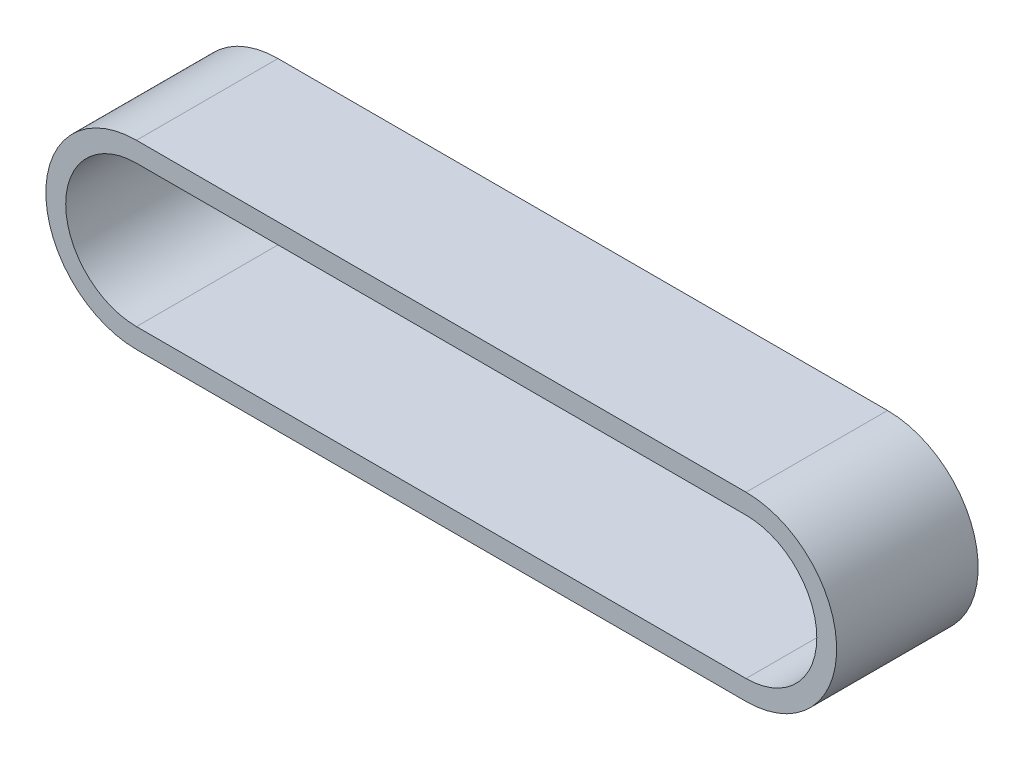
SolidWorks part; units mm, degrees
ref_plane "Plano frontal" through (0, 0, 0) normal (0, 0, 1) x (1, 0, 0)
ref_plane "Plano superior" through (0, 0, 0) normal (0, 1, 0) x (1, 0, 0)
ref_plane "Plano direito" through (0, 0, 0) normal (1, 0, 0) x (0, 0, -1)
sketch "Esboço1" plane through (0, 0, 0) normal (0, 0, 1) x (1, 0, 0)
  line L0 (0, 0) -> (107.6828, 0)
  line L2 (0, -25) -> (107.6828, -25)
  line L4 (0, 3.509) -> (107.6828, 3.509)
  line L6 (0, -28.509) -> (107.6828, -28.509)
  arc A1 (0, 0) -> (0, -25) centre (0, -12.5) ccw
  arc A2 (107.6828, 0) -> (107.6828, -25) centre (107.6828, -12.5) cw
  arc A3 (107.6828, 3.509) -> (107.6828, -28.509) centre (107.6828, -12.5) cw
  arc A4 (0, 3.509) -> (0, -28.509) centre (0, -12.5) ccw
  dimension "D1" = 25
extrude "Ressalto-extrusão1" add sketch "Esboço1" along normal blind 25
